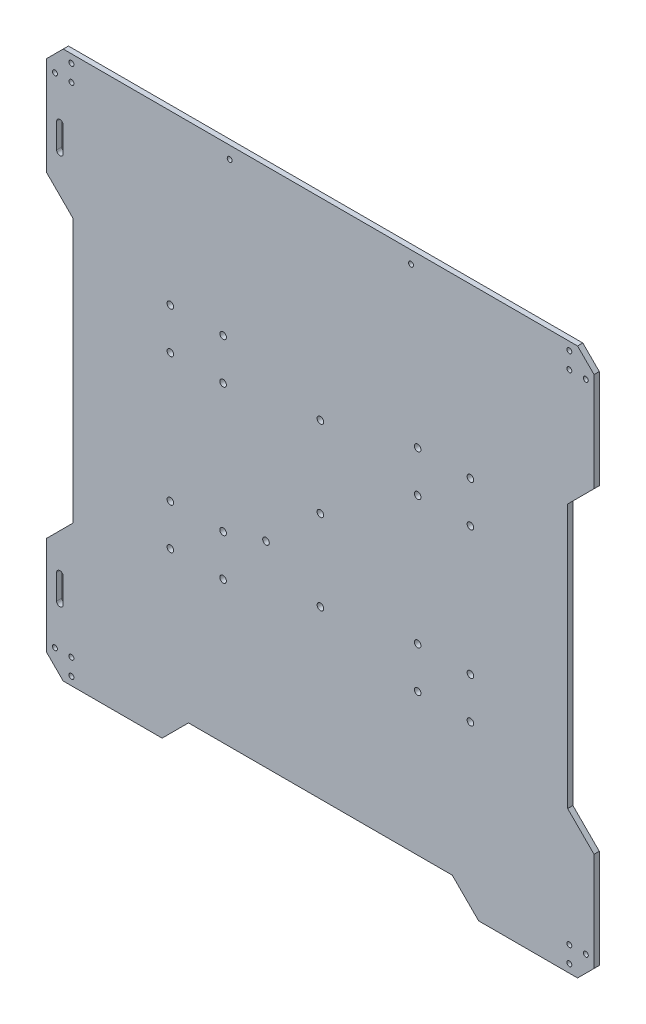
SolidWorks part; units mm, degrees
material "7050-T7651"
ref_plane "Front Plane" through (0, 0, 0) normal (0, 0, 1) x (1, 0, 0)
ref_plane "Top Plane" through (0, 0, 0) normal (0, 1, 0) x (1, 0, 0)
ref_plane "Right Plane" through (0, 0, 0) normal (1, 0, 0) x (0, 0, -1)
sketch "Sketch1" plane through (0, 0, 0) normal (0, 0, 1) x (1, 0, 0)
  line L0 (-161, 161) -> (161, -161) construction
  line L1 (-59, -39) -> (59, 39) construction
  line L2 (-91, 67.5) -> (-59, 67.5) construction
  line L3 (-91, 67.5) -> (-91, 39) construction
  line L4 (-91, 39) -> (-59, 39) construction
  line L5 (-59, 67.5) -> (-59, 39) construction
  line L6 (-91, -39) -> (-59, -39) construction
  line L7 (-91, -39) -> (-91, -67.5) construction
  line L8 (-91, -67.5) -> (-59, -67.5) construction
  line L9 (-59, -39) -> (-59, -67.5) construction
  line L10 (59, -39) -> (91, -39) construction
  line L11 (59, -39) -> (59, -67.5) construction
  line L12 (59, -67.5) -> (91, -67.5) construction
  line L13 (91, -39) -> (91, -67.5) construction
  line L14 (59, 67.5) -> (91, 67.5) construction
  line L15 (59, 67.5) -> (59, 39) construction
  line L16 (59, 39) -> (91, 39) construction
  line L17 (91, 67.5) -> (91, 39) construction
  line L18 (-75, 67.5) -> (-75, 39) construction
  line L19 (-75, -39) -> (-75, -67.5) construction
  line L20 (75, -39) -> (75, -67.5) construction
  line L21 (75, 39) -> (75, 67.5) construction
  line L22 (166, 166) -> (166, 96)
  line L23 (166, 96) -> (150, 80)
  line L24 (150, 80) -> (150, -80)
  line L25 (150, -80) -> (166, -96)
  line L26 (166, -96) -> (166, -166)
  line L27 (166, -166) -> (96, -166)
  line L28 (96, -166) -> (80, -150)
  line L29 (80, -150) -> (-80, -150)
  line L30 (-80, -150) -> (-96, -166)
  line L31 (-96, -166) -> (-166, -166)
  line L32 (-166, -166) -> (-166, -96)
  line L33 (-166, -96) -> (-150, -80)
  line L34 (-150, -80) -> (-150, 80)
  line L35 (-150, 80) -> (-166, 96)
  line L36 (-166, 96) -> (-166, 166)
  line L37 (-166, 166) -> (166, 166)
  line L38 (-55, 158.5) -> (55, 158.5) construction
  line L39 (0, 158.5) -> (0, 0) construction
  line L42 (-27.2213, -27) -> (-12, -27) construction
  line L47 (-7, 32.8786) -> (-7, -22) construction
  line L48 (7, -32.8786) -> (7, 32.8786) construction
  line L49 (0, 49) -> (0, -49) construction
  circle A0 centre (-161, 161) radius 1.5 construction
  circle A1 centre (161, 161) radius 1.5 construction
  circle A2 centre (161, -161) radius 1.5 construction
  circle A3 centre (-161, -161) radius 1.5 construction
  arc A4 (-13.7143, 37.5755) -> (-31.1101, -25.1429) centre (0, 0) ccw construction
  circle A5 centre (-91, 64) radius 2
  circle A6 centre (-91, 39) radius 2
  circle A7 centre (-59, 39) radius 2
  circle A8 centre (-59, 64) radius 2
  circle A9 centre (59, 39) radius 2
  circle A10 centre (59, 64) radius 2
  circle A11 centre (91, 39) radius 2
  circle A12 centre (91, 64) radius 2
  circle A13 centre (59, -64) radius 2
  circle A14 centre (59, -39) radius 2
  circle A15 centre (91, -39) radius 2
  circle A16 centre (91, -64) radius 2
  circle A17 centre (-91, -64) radius 2
  circle A18 centre (-59, -64) radius 2
  circle A19 centre (-59, -39) radius 2
  circle A20 centre (-91, -39) radius 2
  circle A21 centre (-33, -31) radius 2
  arc A22 (13.7143, -37.5755) -> (13.7143, 37.5755) centre (0, 0) ccw construction
  arc A23 (-7, 32.8786) -> (-13.7143, 37.5755) centre (-12, 32.8786) ccw construction
  arc A24 (13.7143, 37.5755) -> (7, 32.8786) centre (12, 32.8786) ccw construction
  arc A25 (7, -32.8786) -> (13.7143, -37.5755) centre (12, -32.8786) ccw construction
  arc A26 (-31.1101, -25.1429) -> (-27.2213, -27) centre (-27.2213, -22) ccw construction
  circle A27 centre (0, 0) radius 2
  circle A28 centre (0, 49) radius 2
  circle A29 centre (0, -49) radius 2
  arc A30 (-7, -22) -> (-12, -27) centre (-12, -22) cw construction
  circle A31 centre (-151, 161) radius 1.5
  circle A32 centre (-161, 151) radius 1.5
  circle A33 centre (151, 161) radius 1.5
  circle A34 centre (161, 151) radius 1.5
  circle A35 centre (161, -151) radius 1.5
  circle A36 centre (151, -161) radius 1.5
  circle A37 centre (-151, -161) radius 1.5
  circle A38 centre (-161, -151) radius 1.5
  circle A39 centre (-151, 151) radius 1.5
  circle A40 centre (151, 151) radius 1.5
  circle A41 centre (151, -151) radius 1.5
  circle A42 centre (-151, -151) radius 1.5
  circle A43 centre (-55, 158.5) radius 1.5
  circle A44 centre (55, 158.5) radius 1.5
  point P97 (7, -39.3827)
  point P129 (-85.0697, 170.2903)
  dimension "D3" = 3
  dimension "D4" = 80
  dimension "D11" = 4
  dimension "D21" = 5
  dimension "D26" = 5
  dimension "D24" = 49
  dimension "D23" = 5
  dimension "D31" = 10
  dimension "D1" = 322
  dimension "D2" = 322
  dimension "D5" = 135
  dimension "D6" = 150
  dimension "D7" = 32
  dimension "D8" = 28.5
  dimension "D9" = 3.5
  dimension "D10" = 3.5
  dimension "D12" = 5
  dimension "D13" = 5
  dimension "D14" = 5
  dimension "D15" = 5
  dimension "D16" = 70
  dimension "D17" = 16
  dimension "D18" = 33
  dimension "D19" = 18
  dimension "D22" = 27
  dimension "D25" = 7
  dimension "D20" = 14
  dimension "D27" = 7
  dimension "D28" = 49
  dimension "D29" = 10
  dimension "D30" = 10
  dimension "D32" = 10
  dimension "D33" = 10
  dimension "D34" = 10
  dimension "D35" = 16
  dimension "D36" = 16
  dimension "D37" = 110
  dimension "D38" = 7.5
extrude "Boss-Extrude1" add sketch "Sketch1" along normal blind 3.175
sketch "Sketch2" plane through (0, 0, 3.175) normal (0, 0, 1) x (1, 0, 0)
  line L0 (-160, 126) -> (-160, 111)
  line L1 (-156, 111) -> (-156, 126)
  line L2 (166, 166) -> (-166, 166) construction
  line L3 (-166, 166) -> (-166, 96) construction
  line L4 (-156, -111) -> (-156, -126)
  line L5 (-160, -126) -> (-160, -111)
  line L6 (-166, -166) -> (-96, -166) construction
  arc A0 (-156, 126) -> (-160, 126) centre (-158, 126) ccw
  arc A1 (-160, 111) -> (-156, 111) centre (-158, 111) ccw
  arc A2 (-156, -111) -> (-160, -111) centre (-158, -111) ccw
  arc A3 (-160, -126) -> (-156, -126) centre (-158, -126) ccw
  dimension "D1" = 4
  dimension "D2" = 40
  dimension "D3" = 15
  dimension "D4" = 8
  dimension "D5" = 40
extrude "Cut-Extrude1" cut sketch "Sketch2" against normal through all
chamfer "Chamfer1" distance 10 angle 45 4 edges at (-166, -166, 1.5875) (166, -166, 1.5875) (-166, 166, 1.5875) (166, 166, 1.5875)
